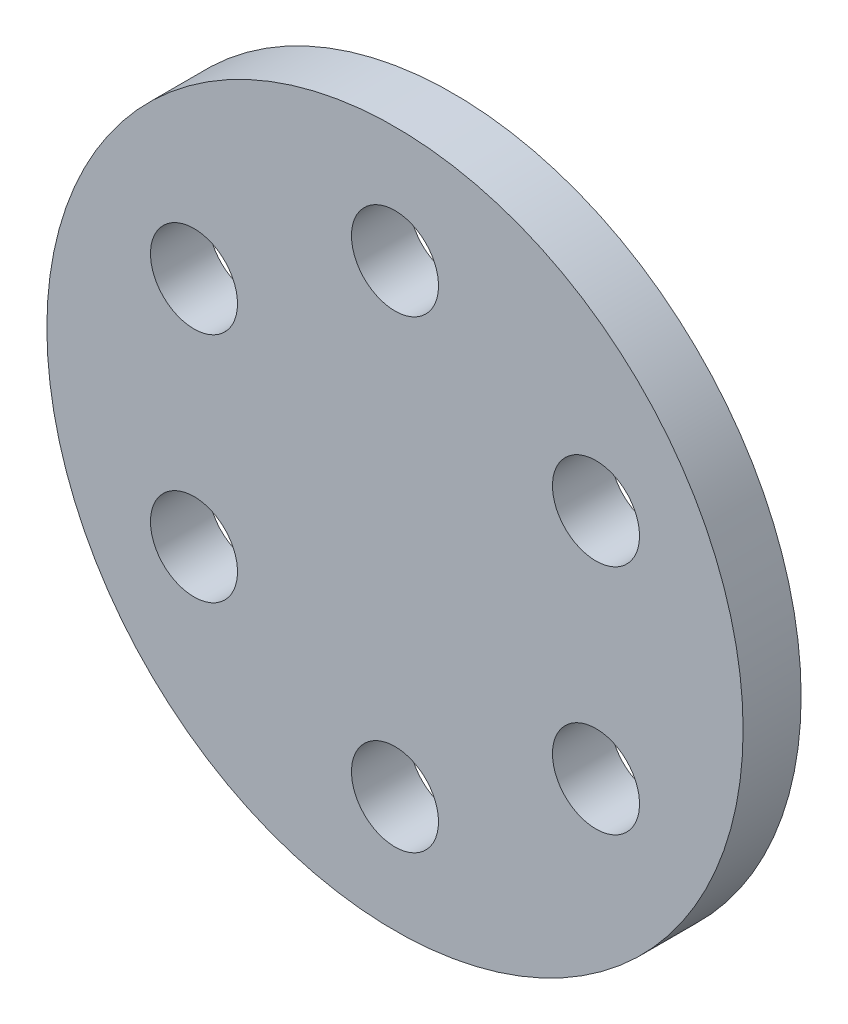
SolidWorks part; units mm, degrees
ref_plane "Přední rovina" through (0, 0, 0) normal (0, 0, 1) x (1, 0, 0)
ref_plane "Horní rovina" through (0, 0, 0) normal (0, 1, 0) x (1, 0, 0)
ref_plane "Pravá rovina" through (0, 0, 0) normal (1, 0, 0) x (0, 0, -1)
sketch "Skica1" plane through (0, 0, 0) normal (0, 0, 1) x (1, 0, 0)
  circle A0 centre (0, 0) radius 60
  dimension "D1" = 120
extrude "Vysunout1" add sketch "Skica1" along normal blind 10
sketch "Skica7" plane through (0, 0, 0) normal (0, 0, -1) x (-1, 0, 0)
  line L0 (0, -60) -> (0, 60) construction
  circle A0 centre (0, 0) radius 40 construction
  circle A1 centre (0, 0) radius 60 construction
  circle A2 centre (0, 40) radius 7.5
  dimension "D1" = 15
  dimension "D2" = 80
extrude "Odebrat vysunutím1" cut sketch "Skica7" against normal through all
pattern_circular "Kruhové pole1" count 6 over 360 about axis through (0, 0, 0) along (0, 0, 1) of "Odebrat vysunutím1"
